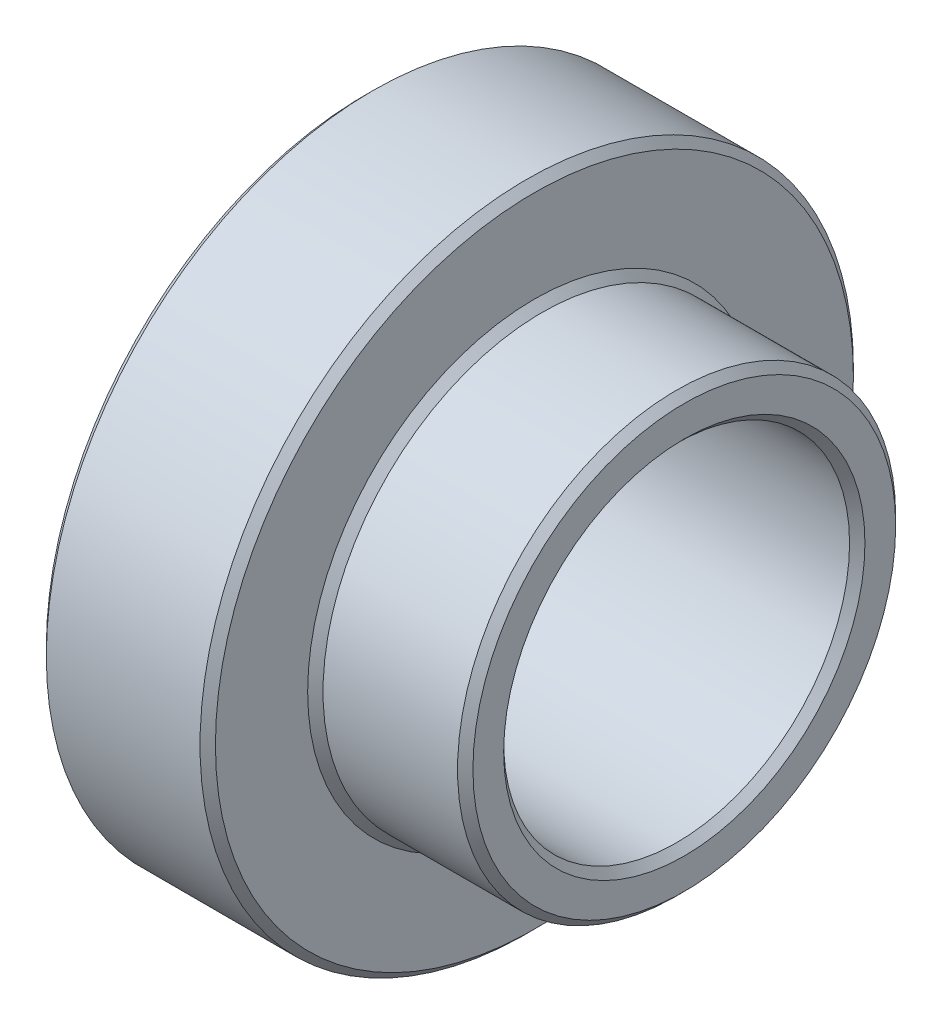
SolidWorks part; units mm, degrees
ref_plane "Front Plane" through (0, 0, 0) normal (0, 0, 1) x (1, 0, 0)
ref_plane "Top Plane" through (0, 0, 0) normal (0, 1, 0) x (1, 0, 0)
ref_plane "Right Plane" through (0, 0, 0) normal (1, 0, 0) x (0, 0, -1)
sketch "Sketch1" plane through (0, 0, 0) normal (0, 0, 1) x (1, 0, 0)
  line L0 (0, 22.5) -> (0, 42.5)
  line L1 (0, 42.5) -> (22, 42.5)
  line L2 (22, 42.5) -> (22, 28.5)
  line L3 (22, 28.5) -> (41.5, 28.5)
  line L4 (41.5, 28.5) -> (41.5, 22.5)
  line L5 (41.5, 22.5) -> (0, 22.5)
  dimension "D1" = 42.5
  dimension "D2" = 28.5
  dimension "D3" = 22.5
  dimension "D4" = 22
  dimension "D5" = 41.5
ref_axis "Axis1" through (43.575, 0, 0) along (-1, 0, 0)
revolve "Revolve1" add sketch "Sketch1" angle 360 about axis through (43.575, 0, 0) along (-1, 0, 0)
chamfer "Chamfer1" distance 1 angle 45 6 edges at (41.5, 0, -28.5) (22, 0, -28.5) (0, 0, -42.5) (22, 0, -42.5) (0, 0, -22.5) (41.5, 0, -22.5)
